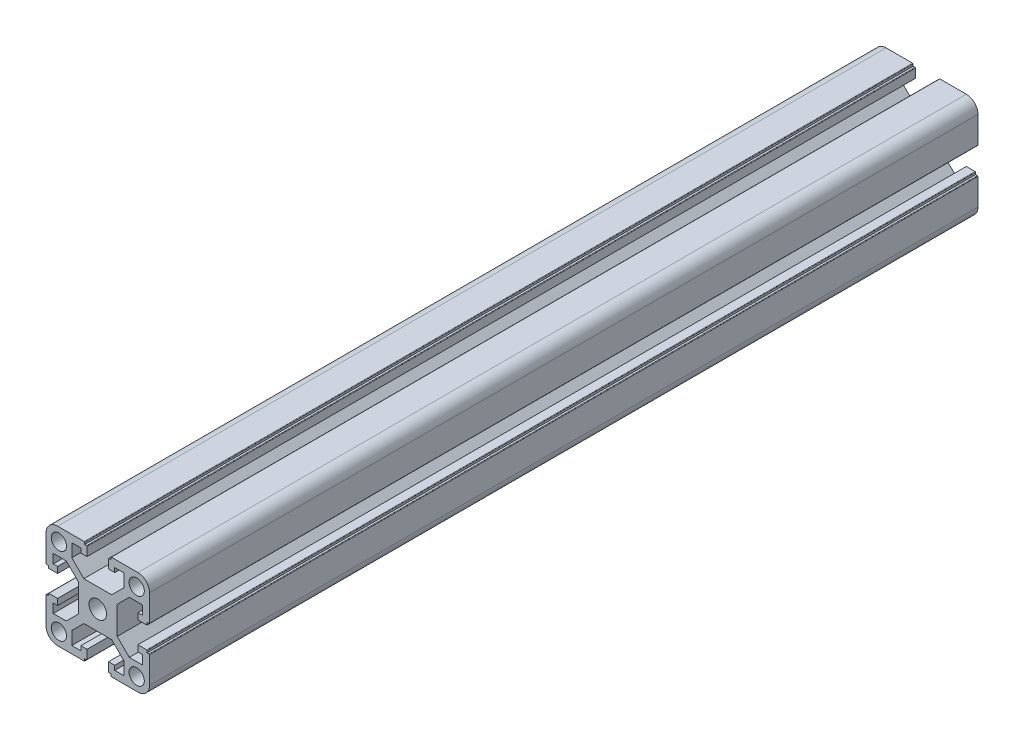
SolidWorks part; units mm, degrees
material "6061-T6 (SS)"
ref_plane "前视基准面" through (0, 0, 0) normal (0, 0, 1) x (1, 0, 0)
ref_plane "上视基准面" through (0, 0, 0) normal (0, 1, 0) x (1, 0, 0)
ref_plane "右视基准面" through (0, 0, 0) normal (1, 0, 0) x (0, 0, -1)
ref_plane "基准面1" through (0, 0, 50) normal (0, 0, 1) x (1, 0, 0)
sketch "草图1" plane through (0, 0, 50) normal (0, 0, 1) x (1, 0, 0)
  line L0 (-1518.245, 3588.0043) -> (-1518.245, 3582.9756)
  line L1 (-1518.245, 3582.9756) -> (-1522.9163, 3578.3043)
  line L2 (-1522.9163, 3578.3043) -> (-1533.6737, 3578.3043)
  line L3 (-1533.6737, 3578.3043) -> (-1538.345, 3582.9756)
  line L4 (-1538.345, 3582.9756) -> (-1538.345, 3588.0043)
  line L5 (-1538.345, 3588.0043) -> (-1534.845, 3588.0043)
  line L6 (-1534.845, 3588.0043) -> (-1534.845, 3586.3043)
  line L7 (-1534.845, 3586.3043) -> (-1532.445, 3586.3043)
  line L8 (-1532.445, 3586.3043) -> (-1532.445, 3589.7043)
  line L9 (-1532.645, 3589.9043) -> (-1533.345, 3589.9043)
  line L10 (-1533.345, 3589.9043) -> (-1533.345, 3590.6043)
  line L11 (-1533.545, 3590.8043) -> (-1543.795, 3590.8043)
  line L12 (-1548.295, 3586.3043) -> (-1548.295, 3576.0543)
  line L13 (-1548.095, 3575.8543) -> (-1547.395, 3575.8543)
  line L14 (-1547.395, 3575.8543) -> (-1547.395, 3575.1543)
  line L15 (-1547.195, 3574.9543) -> (-1543.795, 3574.9543)
  line L16 (-1543.795, 3574.9543) -> (-1543.795, 3577.3543)
  line L17 (-1543.795, 3577.3543) -> (-1545.495, 3577.3543)
  line L18 (-1545.495, 3577.3543) -> (-1545.495, 3580.8543)
  line L19 (-1545.495, 3580.8543) -> (-1540.4663, 3580.8543)
  line L20 (-1540.4663, 3580.8543) -> (-1535.795, 3576.183)
  line L21 (-1535.795, 3576.183) -> (-1535.795, 3565.4256)
  line L22 (-1535.795, 3565.4256) -> (-1540.4663, 3560.7543)
  line L23 (-1540.4663, 3560.7543) -> (-1545.495, 3560.7543)
  line L24 (-1545.495, 3560.7543) -> (-1545.495, 3564.2543)
  line L25 (-1545.495, 3564.2543) -> (-1543.795, 3564.2543)
  line L26 (-1543.795, 3564.2543) -> (-1543.795, 3566.6543)
  line L27 (-1543.795, 3566.6543) -> (-1547.195, 3566.6543)
  line L28 (-1547.395, 3566.4543) -> (-1547.395, 3565.7543)
  line L29 (-1547.395, 3565.7543) -> (-1548.095, 3565.7543)
  line L30 (-1548.295, 3565.5543) -> (-1548.295, 3555.3043)
  line L31 (-1543.795, 3550.8043) -> (-1533.545, 3550.8043)
  line L32 (-1533.345, 3551.0043) -> (-1533.345, 3551.7043)
  line L33 (-1533.345, 3551.7043) -> (-1532.645, 3551.7043)
  line L34 (-1532.445, 3551.9043) -> (-1532.445, 3555.3043)
  line L35 (-1532.445, 3555.3043) -> (-1534.845, 3555.3043)
  line L36 (-1534.845, 3555.3043) -> (-1534.845, 3553.6043)
  line L37 (-1534.845, 3553.6043) -> (-1538.345, 3553.6043)
  line L38 (-1538.345, 3553.6043) -> (-1538.345, 3558.633)
  line L39 (-1538.345, 3558.633) -> (-1533.6737, 3563.3043)
  line L40 (-1533.6737, 3563.3043) -> (-1522.9163, 3563.3043)
  line L41 (-1522.9163, 3563.3043) -> (-1518.245, 3558.633)
  line L42 (-1518.245, 3558.633) -> (-1518.245, 3553.6043)
  line L43 (-1518.245, 3553.6043) -> (-1521.745, 3553.6043)
  line L44 (-1521.745, 3553.6043) -> (-1521.745, 3555.3043)
  line L45 (-1521.745, 3555.3043) -> (-1524.145, 3555.3043)
  line L46 (-1524.145, 3555.3043) -> (-1524.145, 3551.9043)
  line L47 (-1523.945, 3551.7043) -> (-1523.245, 3551.7043)
  line L48 (-1523.245, 3551.7043) -> (-1523.245, 3551.0043)
  line L49 (-1523.045, 3550.8043) -> (-1512.795, 3550.8043)
  line L50 (-1508.295, 3555.3043) -> (-1508.295, 3565.5543)
  line L51 (-1508.495, 3565.7543) -> (-1509.195, 3565.7543)
  line L52 (-1509.195, 3565.7543) -> (-1509.195, 3566.4543)
  line L53 (-1509.395, 3566.6543) -> (-1512.795, 3566.6543)
  line L54 (-1512.795, 3566.6543) -> (-1512.795, 3564.2543)
  line L55 (-1512.795, 3564.2543) -> (-1511.095, 3564.2543)
  line L56 (-1511.095, 3564.2543) -> (-1511.095, 3560.7543)
  line L57 (-1511.095, 3560.7543) -> (-1516.1237, 3560.7543)
  line L58 (-1516.1237, 3560.7543) -> (-1520.795, 3565.4256)
  line L59 (-1520.795, 3565.4256) -> (-1520.795, 3576.183)
  line L60 (-1520.795, 3576.183) -> (-1516.1237, 3580.8543)
  line L61 (-1516.1237, 3580.8543) -> (-1511.095, 3580.8543)
  line L62 (-1511.095, 3580.8543) -> (-1511.095, 3577.3543)
  line L63 (-1511.095, 3577.3543) -> (-1512.795, 3577.3543)
  line L64 (-1512.795, 3577.3543) -> (-1512.795, 3574.9543)
  line L65 (-1512.795, 3574.9543) -> (-1509.395, 3574.9543)
  line L66 (-1509.195, 3575.1543) -> (-1509.195, 3575.8543)
  line L67 (-1509.195, 3575.8543) -> (-1508.495, 3575.8543)
  line L68 (-1508.295, 3576.0543) -> (-1508.295, 3586.3043)
  line L69 (-1512.795, 3590.8043) -> (-1523.045, 3590.8043)
  line L70 (-1523.245, 3590.6043) -> (-1523.245, 3589.9043)
  line L71 (-1523.245, 3589.9043) -> (-1523.945, 3589.9043)
  line L72 (-1524.145, 3589.7043) -> (-1524.145, 3586.3043)
  line L73 (-1524.145, 3586.3043) -> (-1521.745, 3586.3043)
  line L74 (-1521.745, 3586.3043) -> (-1521.745, 3588.0043)
  line L75 (-1521.745, 3588.0043) -> (-1518.245, 3588.0043)
  circle A0 centre (-1513.27, 3555.7793) radius 2.95
  circle A1 centre (-1528.295, 3570.8043) radius 3.4
  circle A2 centre (-1513.27, 3585.8293) radius 2.95
  arc A3 (-1532.445, 3589.7043) -> (-1532.645, 3589.9043) centre (-1532.645, 3589.7043) ccw
  arc A4 (-1533.345, 3590.6043) -> (-1533.545, 3590.8043) centre (-1533.545, 3590.6043) ccw
  arc A5 (-1543.795, 3590.8043) -> (-1548.295, 3586.3043) centre (-1543.795, 3586.3043) ccw
  arc A6 (-1548.295, 3576.0543) -> (-1548.095, 3575.8543) centre (-1548.095, 3576.0543) ccw
  arc A7 (-1547.395, 3575.1543) -> (-1547.195, 3574.9543) centre (-1547.195, 3575.1543) ccw
  arc A8 (-1547.195, 3566.6543) -> (-1547.395, 3566.4543) centre (-1547.195, 3566.4543) ccw
  arc A9 (-1548.095, 3565.7543) -> (-1548.295, 3565.5543) centre (-1548.095, 3565.5543) ccw
  arc A10 (-1548.295, 3555.3043) -> (-1543.795, 3550.8043) centre (-1543.795, 3555.3043) ccw
  arc A11 (-1533.545, 3550.8043) -> (-1533.345, 3551.0043) centre (-1533.545, 3551.0043) ccw
  arc A12 (-1532.645, 3551.7043) -> (-1532.445, 3551.9043) centre (-1532.645, 3551.9043) ccw
  arc A13 (-1524.145, 3551.9043) -> (-1523.945, 3551.7043) centre (-1523.945, 3551.9043) ccw
  arc A14 (-1523.245, 3551.0043) -> (-1523.045, 3550.8043) centre (-1523.045, 3551.0043) ccw
  arc A15 (-1512.795, 3550.8043) -> (-1508.295, 3555.3043) centre (-1512.795, 3555.3043) ccw
  arc A16 (-1508.295, 3565.5543) -> (-1508.495, 3565.7543) centre (-1508.495, 3565.5543) ccw
  arc A17 (-1509.195, 3566.4543) -> (-1509.395, 3566.6543) centre (-1509.395, 3566.4543) ccw
  arc A18 (-1509.395, 3574.9543) -> (-1509.195, 3575.1543) centre (-1509.395, 3575.1543) ccw
  arc A19 (-1508.495, 3575.8543) -> (-1508.295, 3576.0543) centre (-1508.495, 3576.0543) ccw
  arc A20 (-1508.295, 3586.3043) -> (-1512.795, 3590.8043) centre (-1512.795, 3586.3043) ccw
  arc A21 (-1523.045, 3590.8043) -> (-1523.245, 3590.6043) centre (-1523.045, 3590.6043) ccw
  arc A22 (-1523.945, 3589.9043) -> (-1524.145, 3589.7043) centre (-1523.945, 3589.7043) ccw
  circle A23 centre (-1543.32, 3585.8293) radius 2.95
  circle A24 centre (-1543.32, 3555.7793) radius 2.95
extrude "凸台-拉伸1" add sketch "草图1" against normal mid plane 320
ref_plane "基准面2" through (-1528.295, 0, 0) normal (1, 0, 0) x (0, 0, -1)
ref_plane "基准面3" through (0, 3570.8043, 0) normal (0, 1, 0) x (1, 0, 0)
